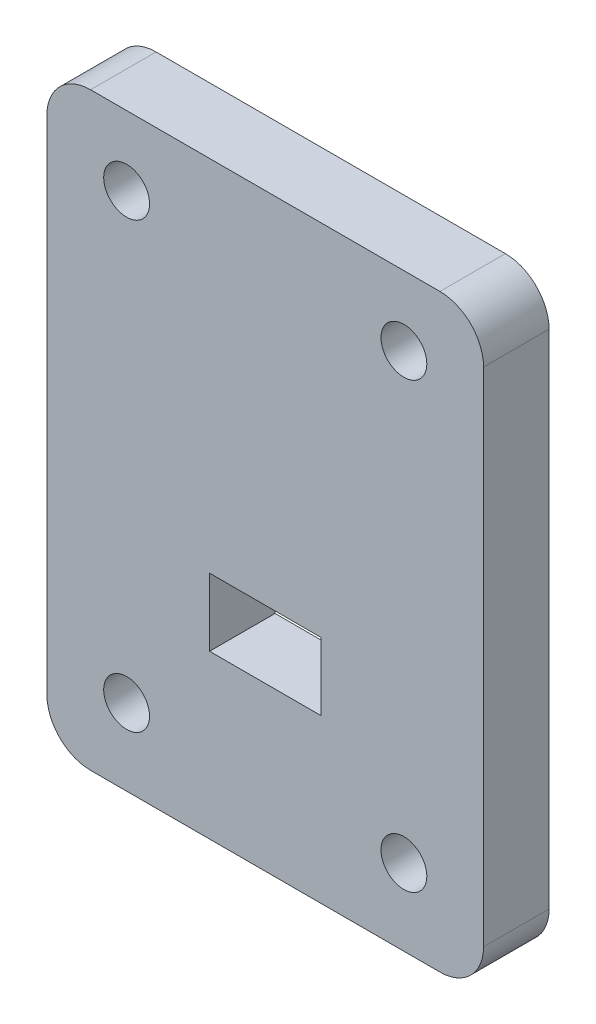
SolidWorks part; units mm, degrees
ref_plane "Alzado" through (0, 0, 0) normal (0, 0, 1) x (1, 0, 0)
ref_plane "Planta" through (0, 0, 0) normal (0, 1, 0) x (1, 0, 0)
ref_plane "Vista lateral" through (0, 0, 0) normal (1, 0, 0) x (0, 0, -1)
sketch "Croquis1" plane through (0, 0, 0) normal (0, 0, 1) x (1, 0, 0)
  line L1 (-10, -13.5) -> (10, -13.5)
  line L2 (-10, -13.5) -> (-10, 13.5)
  line L3 (-10, 13.5) -> (10, 13.5)
  line L4 (10, -13.5) -> (10, 13.5)
  line L5 (-10, -13.5) -> (10, 13.5) construction
  line L6 (-10, 13.5) -> (10, -13.5) construction
  point P0 (0, 0)
  dimension "D1" = 20
  dimension "D2" = 27
extrude "Saliente-Extruir1" add sketch "Croquis1" along normal blind 3
sketch "Croquis2" plane through (0, 0, 3) normal (0, 0, 1) x (1, 0, 0)
  line L1 (-2.55, -6.05) -> (2.55, -6.05)
  line L2 (-2.55, -6.05) -> (-2.55, -2.95)
  line L3 (-2.55, -2.95) -> (2.55, -2.95)
  line L4 (2.55, -6.05) -> (2.55, -2.95)
  line L5 (-2.55, -6.05) -> (2.55, -2.95) construction
  line L6 (-2.55, -2.95) -> (2.55, -6.05) construction
  line L7 (-10, -13.5) -> (10, -13.5) construction
  point P0 (0, -4.5)
  point P5 (0, 0)
  dimension "D1" = 3.1
  dimension "D2" = 5.1
  dimension "D3" = 9
extrude "Cortar-Extruir1" cut sketch "Croquis2" against normal blind 10
sketch "Croquis3" plane through (0, 0, 3) normal (0, 0, 1) x (1, 0, 0)
  line L0 (-6.35, 10.32) -> (-6.35, -10) construction
  line L1 (-6.35, -10) -> (6.35, -10) construction
  line L2 (6.35, -10) -> (6.35, 10.32) construction
  line L3 (6.35, 10.32) -> (-6.35, 10.32) construction
  line L4 (0, 0) -> (0, -10) construction
  line L5 (-10, -13.5) -> (10, -13.5) construction
  circle A0 centre (-6.35, 10.32) radius 1.05
  circle A1 centre (6.35, 10.32) radius 1.05
  circle A2 centre (6.35, -10) radius 1.05
  circle A3 centre (-6.35, -10) radius 1.05
  dimension "D1" = 2.1
  dimension "D2" = 12.7
  dimension "D3" = 20.32
  dimension "D4" = 3.5
extrude "Cortar-Extruir2" cut sketch "Croquis3" against normal blind 10
fillet "Redondeo1" radius 2 4 edges at (-10, 13.5, 1.5) (10, 13.5, 1.5) (10, -13.5, 1.5) (-10, -13.5, 1.5)
